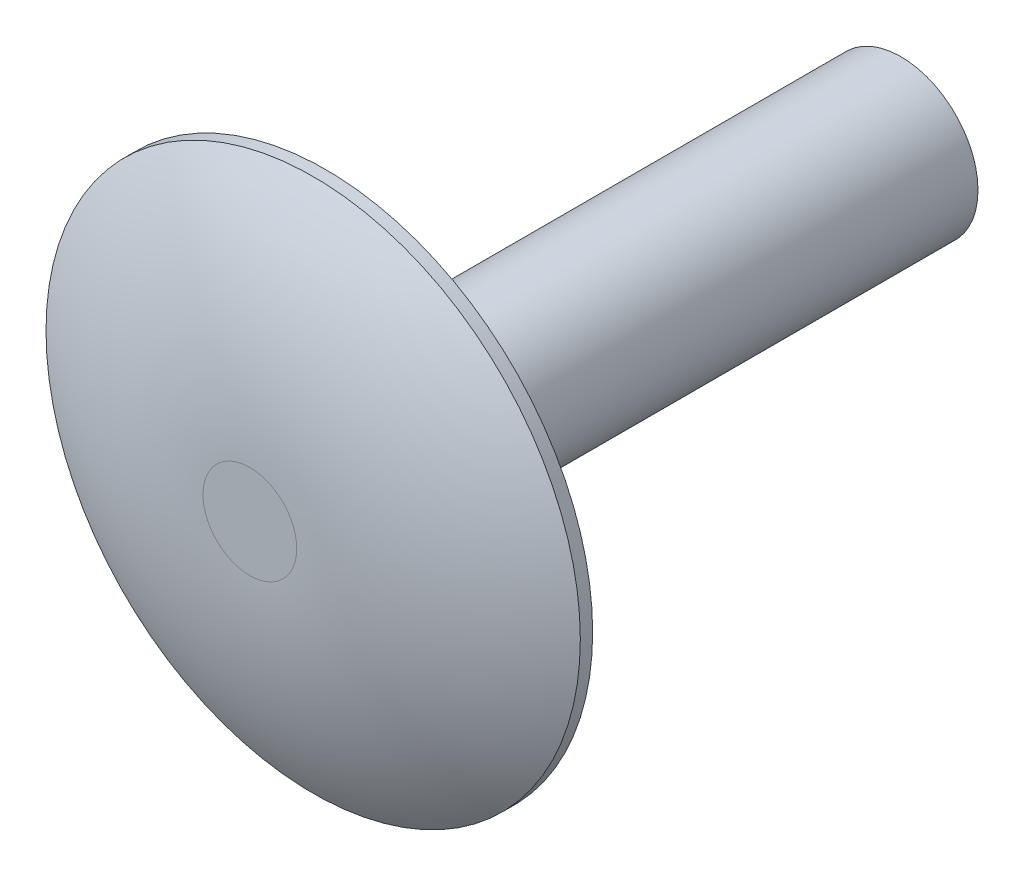
SolidWorks part; units mm, degrees
material "6061 Alloy"
ref_plane "Front Plane" through (0, 0, 0) normal (0, 0, 1) x (1, 0, 0)
ref_plane "Top Plane" through (0, 0, 0) normal (0, 1, 0) x (1, 0, 0)
ref_plane "Right Plane" through (0, 0, 0) normal (1, 0, 0) x (0, 0, -1)
sketch "Sketch1" plane through (0, 0, 0) normal (0, 0, 1) x (1, 0, 0)
  circle A0 centre (0, 0) radius 8.255
  dimension "D1" = 16.51
extrude "Boss-Extrude1" add sketch "Sketch1" along normal blind 2.3368
sketch "Sketch2" plane through (0, 0, 0) normal (0, 0, 1) x (1, 0, 0)
  circle A0 centre (0, 0) radius 2.3813
  dimension "D1" = 4.7625
extrude "Boss-Extrude2" add sketch "Sketch2" against normal blind 17.78
sketch "Sketch3" plane through (0, 0, 0) normal (0, 1, 0) x (1, 0, 0)
  line L0 (0, -2.3368) -> (1.4478, -2.3368)
  line L1 (-8.255, -2.3368) -> (8.255, -2.3368) construction
  line L2 (0, -2.3368) -> (0, 0) construction
  line L3 (8.255, -2.3368) -> (8.255, 0) construction
  line L4 (8.255, -0.381) -> (8.255, 0)
  line L5 (8.255, 0) -> (-8.255, 0) construction
  line L6 (8.255, -0.381) -> (8.255, -2.3368)
  line L7 (8.255, -2.3368) -> (1.4478, -2.3368)
  arc A0 (1.4478, -2.3368) -> (8.255, -0.381) centre (1.4478, 10.4874) ccw
  dimension "D1" = 2.8956
  dimension "D2" = 0.381
revolve "Cut-Revolve1" cut sketch "Sketch3" angle 360 about L2
